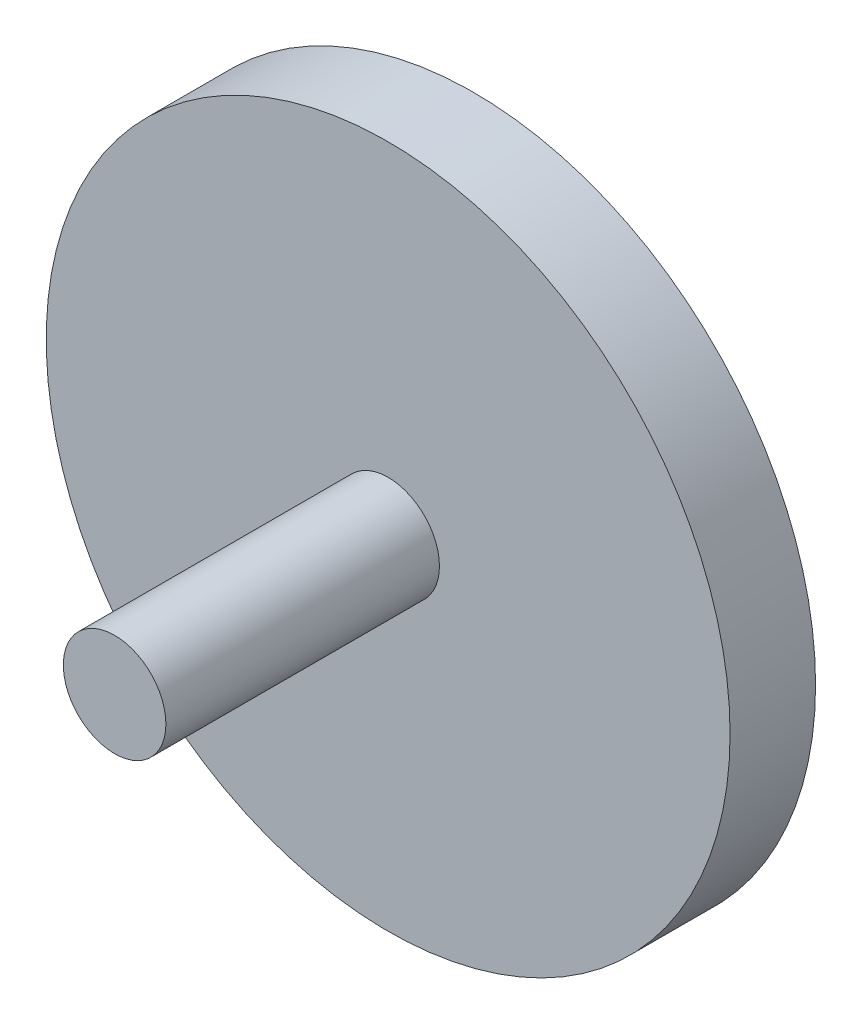
SolidWorks part; units mm, degrees
ref_plane "Front Plane" through (0, 0, 0) normal (0, 0, 1) x (1, 0, 0)
ref_plane "Top Plane" through (0, 0, 0) normal (0, 1, 0) x (1, 0, 0)
ref_plane "Right Plane" through (0, 0, 0) normal (1, 0, 0) x (0, 0, -1)
sketch "Sketch1" plane through (0, 0, 0) normal (0, 0, 1) x (1, 0, 0)
  circle A0 centre (0, 0) radius 100
  dimension "D1" = 200
extrude "Boss-Extrude1" add sketch "Sketch1" along normal blind 25
sketch "Sketch2" plane through (0, 0, 25) normal (0, 0, 1) x (1, 0, 0)
  circle A0 centre (0, 0) radius 15
  dimension "D1" = 30
extrude "Boss-Extrude2" add sketch "Sketch2" along normal blind 80 contours A0
sketch "Sketch3" plane through (0, 0, 0) normal (0, 0, -1) x (-1, 0, 0)
  circle A0 centre (0, 50) radius 10
  dimension "D1" = 20
  dimension "D2" = 50
extrude "Cut-Extrude1" cut sketch "Sketch3" against normal blind 5 contours A0
